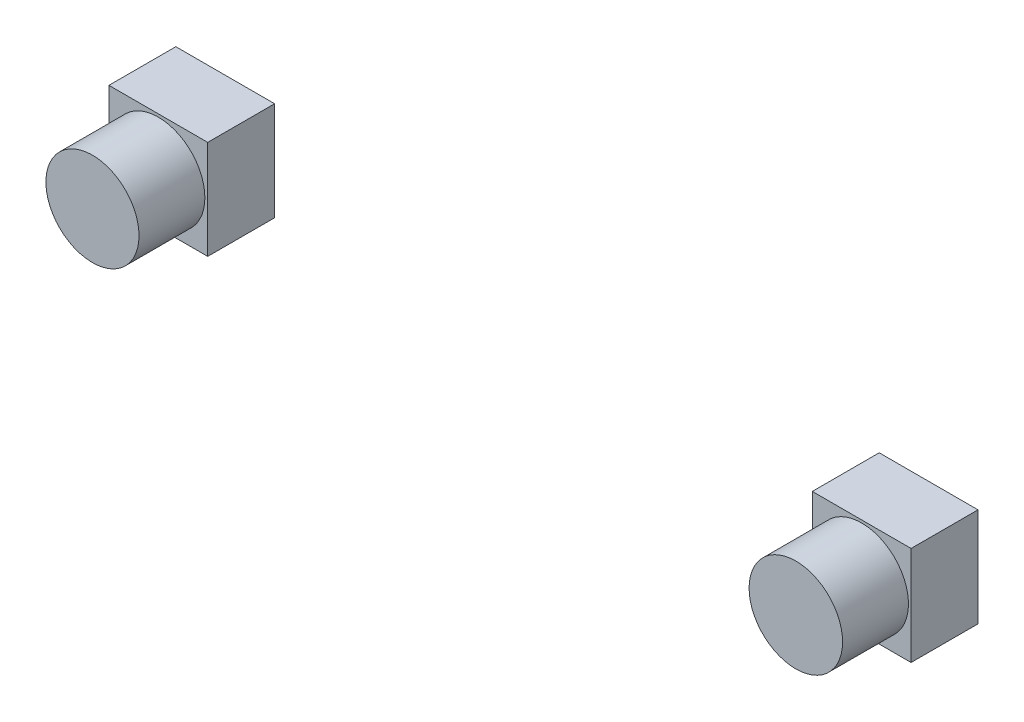
SolidWorks part; units mm, degrees
ref_plane "Front Plane" through (0, 0, 0) normal (0, 0, 1) x (1, 0, 0)
ref_plane "Top Plane" through (0, 0, 0) normal (0, 1, 0) x (1, 0, 0)
ref_plane "Right Plane" through (0, 0, 0) normal (1, 0, 0) x (0, 0, -1)
sketch "Sketch1" plane through (0, 0, 0) normal (0, 0, 1) x (1, 0, 0)
  line L1 (305, 710.27) -> (230, 710.27)
  line L2 (305, 710.27) -> (305, 635.27)
  line L3 (305, 635.27) -> (230, 635.27)
  line L4 (230, 710.27) -> (230, 635.27)
  line L5 (-304, 710.27) -> (-229, 710.27)
  line L6 (-304, 710.27) -> (-304, 635.27)
  line L7 (-304, 635.27) -> (-229, 635.27)
  line L8 (-229, 710.27) -> (-229, 635.27)
  dimension "D1" = 75
  dimension "D2" = 75
  dimension "D3" = 75
  dimension "D4" = 75
extrude "Boss-Extrude1" add sketch "Sketch1" along normal blind 50.8
sketch "Sketch2" plane through (0, 0, 50.8) normal (0, 0, 1) x (1, 0, 0)
  line L0 (230, 672.77) -> (305, 672.77) construction
  line L1 (230, 710.27) -> (230, 635.27) construction
  line L2 (305, 635.27) -> (305, 710.27) construction
  line L3 (-266.5, 710.27) -> (-266.5, 635.27) construction
  line L4 (230, 635.27) -> (305, 635.27) construction
  line L5 (267.5, 635.27) -> (267.5, 710.27) construction
  line L6 (305, 710.27) -> (230, 710.27) construction
  line L7 (-229, 710.27) -> (-304, 710.27) construction
  line L8 (-304, 635.27) -> (-229, 635.27) construction
  line L10 (-304, 710.27) -> (-304, 635.27) construction
  line L11 (-304, 672.77) -> (-229, 672.77) construction
  line L12 (-229, 635.27) -> (-229, 710.27) construction
  circle A0 centre (267.5, 672.77) radius 35.4886
  circle A1 centre (-266.5, 672.77) radius 35.3414
  dimension "D1" = 70.9772
  dimension "D2" = 70.6827
extrude "Boss-Extrude2" add sketch "Sketch2" along normal blind 50
